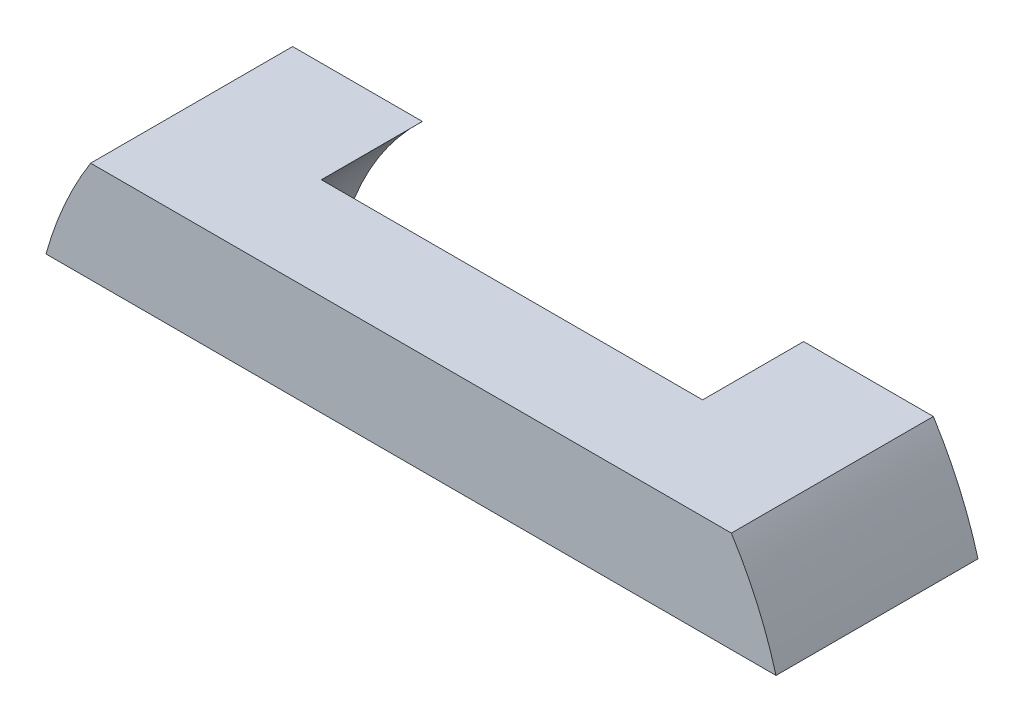
SolidWorks part; units mm, degrees
ref_plane "Front Plane" through (0, 0, 0) normal (0, 0, 1) x (1, 0, 0)
ref_plane "Top Plane" through (0, 0, 0) normal (0, 1, 0) x (1, 0, 0)
ref_plane "Right Plane" through (0, 0, 0) normal (1, 0, 0) x (0, 0, -1)
sketch "Sketch3" plane through (0, 0, 0) normal (0, 0, 1) x (1, 0, 0)
  line L0 (0, 0) -> (0, 14.5651) construction
  line L1 (-10.0716, 6.35) -> (10.0716, 6.35)
  line L3 (-11.4751, 3.175) -> (11.4751, 3.175)
  arc A0 (-8.1335, 3.175) -> (-5.9927, 6.35) centre (0, 0) ccw construction
  circle A1 centre (0, 0) radius 11.9062 construction
  arc A2 (11.4751, 3.175) -> (10.0716, 6.35) centre (0, 0) ccw
  arc A3 (-11.4751, 3.175) -> (-10.0716, 6.35) centre (0, 0) cw
  circle A4 centre (0, 0) radius 8.7313 construction
  dimension "D1" = 17.4625
  dimension "D3" = 3.175
  dimension "D4" = 3.175
  dimension "D2" = 3.175
extrude "Boss-Extrude2" add sketch "Sketch3" along normal blind 6.35
sketch "Sketch5" plane through (0, 0, 0) normal (0, 0, -1) x (-1, 0, 0)
  circle A0 centre (0, 0) radius 8.7312
  dimension "D1" = 17.4625
extrude "Cut-Extrude1" cut sketch "Sketch5" against normal blind 3.175
